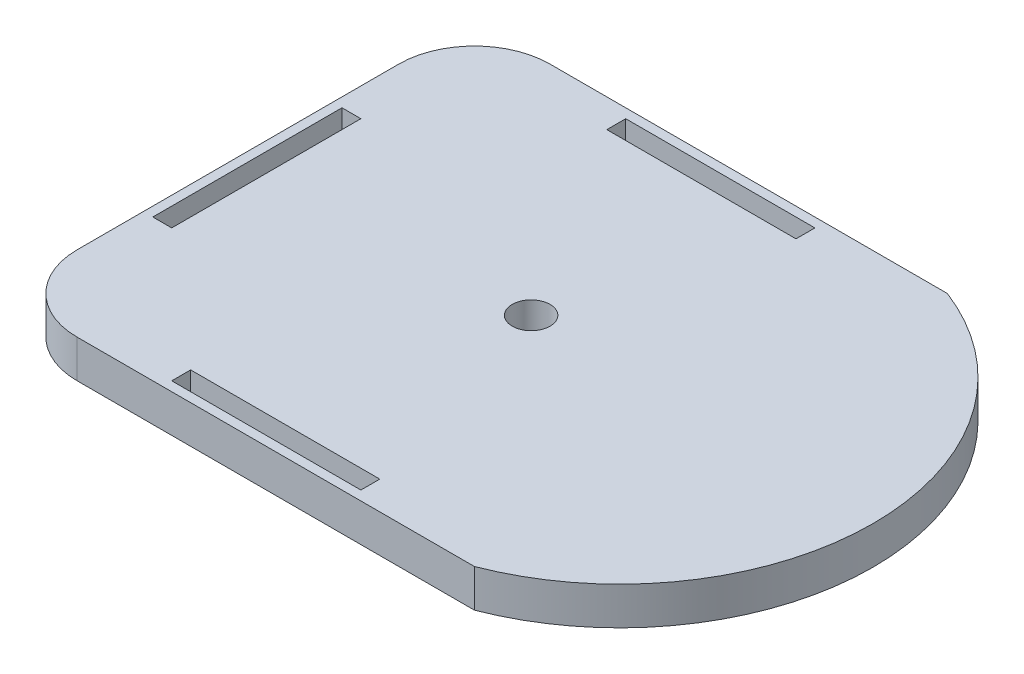
SolidWorks part; units mm, degrees
ref_plane "Ön Düzlem" through (0, 0, 0) normal (0, 0, 1) x (1, 0, 0)
ref_plane "Üst Düzlem" through (0, 0, 0) normal (0, 1, 0) x (1, 0, 0)
ref_plane "Sağ Düzlem" through (0, 0, 0) normal (1, 0, 0) x (0, 0, -1)
sketch "Çizim1" plane through (0, 0, 0) normal (0, 1, 0) x (1, 0, 0)
  line L0 (-41.1253, 193.8804) -> (168.8747, 193.8804)
  line L1 (-81.1253, 153.8804) -> (-81.1253, -16.1196)
  line L2 (-41.1253, -56.1196) -> (168.8747, -56.1196)
  arc A0 (-81.1253, -16.1196) -> (-41.1253, -56.1196) centre (-41.1253, -16.1196) ccw
  arc A1 (-41.1253, 193.8804) -> (-81.1253, 153.8804) centre (-41.1253, 153.8804) ccw
  arc A2 (168.8747, 193.8804) -> (168.8747, -56.1196) centre (120.6083, 68.8804) cw
  point P0 (0, 0)
  dimension "D1" = 40
  dimension "D4" = 250
  dimension "D5" = 133.9949
  dimension "D2" = 250
  dimension "D3" = 250
extrude "Yükseklik-Ekstrüzyon1" add sketch "Çizim1" along normal blind 20
sketch "Çizim2" plane through (0, 20, 0) normal (0, 1, 0) x (1, 0, 0)
  line L0 (294.4799, 68.8804) -> (-156.7306, 68.8804) construction
  line L1 (3.8747, 188.8804) -> (103.8747, 188.8804)
  line L2 (3.8747, 188.8804) -> (3.8747, 178.8804)
  line L3 (3.8747, 178.8804) -> (103.8747, 178.8804)
  line L4 (103.8747, 188.8804) -> (103.8747, 178.8804)
  line L5 (-76.1253, 118.8804) -> (-66.1253, 118.8804)
  line L6 (-76.1253, 118.8804) -> (-76.1253, 18.8804)
  line L7 (-76.1253, 18.8804) -> (-66.1253, 18.8804)
  line L8 (-66.1253, 118.8804) -> (-66.1253, 18.8804)
  line L9 (168.8747, 193.8804) -> (-41.1253, 193.8804) construction
  line L10 (-81.1253, 153.8804) -> (-81.1253, -16.1196) construction
  line L11 (3.8747, -41.1196) -> (103.8747, -41.1196)
  line L12 (103.8747, -51.1196) -> (103.8747, -41.1196)
  line L13 (3.8747, -51.1196) -> (103.8747, -51.1196)
  line L14 (3.8747, -51.1196) -> (3.8747, -41.1196)
  dimension "D1" = 5
  dimension "D2" = 5
  dimension "D3" = 10
  dimension "D4" = 100
  dimension "D5" = 100
  dimension "D6" = 10
  dimension "D7" = 50
  dimension "D10" = 85
  dimension "D11" = 85
extrude "Kes-Ekstrüzyon1" cut sketch "Çizim2" against normal blind 12.5
sketch "Çizim4" plane through (0, 20, 0) normal (0, 1, 0) x (1, 0, 0)
  line L0 (-81.1253, 153.8804) -> (-81.1253, -16.1196) construction
  line L4 (168.8747, 193.8804) -> (-41.1253, 193.8804) construction
  circle A0 centre (68.8747, 73.8804) radius 10
  dimension "D1" = 20
  dimension "D2" = 150
  dimension "D3" = 120
extrude "Kes-Ekstrüzyon2" cut sketch "Çizim4" against normal blind 230.5
